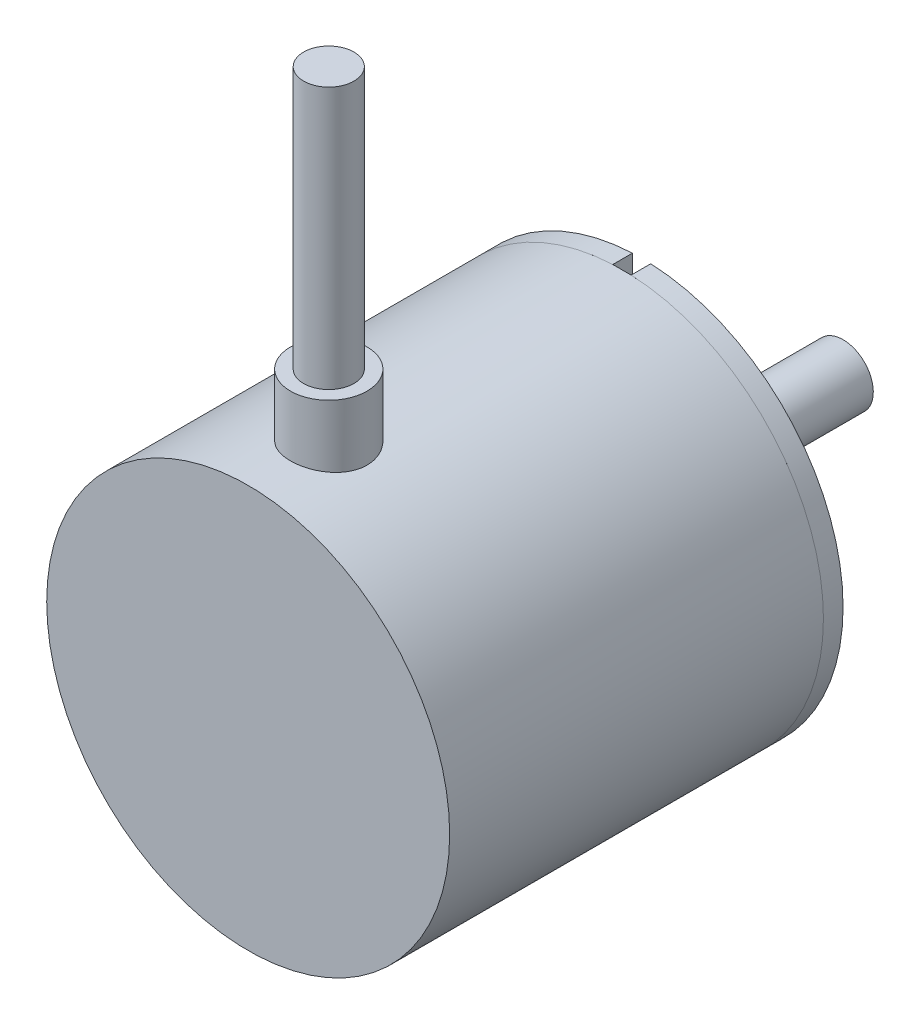
SolidWorks part; units mm, degrees
ref_plane "Front Plane" through (0, 0, 0) normal (0, 0, 1) x (1, 0, 0)
ref_plane "Top Plane" through (0, 0, 0) normal (0, 1, 0) x (1, 0, 0)
ref_plane "Right Plane" through (0, 0, 0) normal (1, 0, 0) x (0, 0, -1)
sketch "Sketch1" plane through (0, 0, 0) normal (0, 0, 1) x (1, 0, 0)
  circle A0 centre (0, 0) radius 20
extrude "Boss-Extrude1" add sketch "Sketch1" along normal blind 1.95
sketch "Sketch2" plane through (0, 0, 0) normal (0, 0, -1) x (-1, 0, 0)
  circle A0 centre (0, 0) radius 10
extrude "Boss-Extrude2" add sketch "Sketch2" along normal blind 5
sketch "Sketch3" plane through (0, 0, -5) normal (0, 0, -1) x (-1, 0, 0)
  circle A0 centre (0, 0) radius 3
extrude "Boss-Extrude3" add sketch "Sketch3" along normal blind 15
sketch "Sketch4" plane through (0, 0, 0) normal (0, 0, -1) x (-1, 0, 0)
  line L0 (0, 15) -> (-12.9904, -7.5) construction
  circle A0 centre (0, 0) radius 15 construction
  circle A1 centre (0, 15) radius 1
  circle A2 centre (12.9904, -7.5) radius 1
  circle A3 centre (-12.9904, -7.5) radius 1
  point P11 (0, 0.1678)
  point P12 (0, 0)
  dimension "D1" = 3
extrude "Cut-Extrude1" cut sketch "Sketch4" against normal blind 10
sketch "Sketch5" plane through (0, 0, 0) normal (0, 0, -1) x (-1, 0, 0)
  line L0 (0.91, 20) -> (-0.91, 20)
  line L1 (0, 20) -> (0, 18.0795)
  line L2 (-0.91, 20) -> (-0.91, 18.0795)
  line L3 (-0.91, 18.0795) -> (0.91, 18.0795)
  line L4 (0.91, 20) -> (0.91, 18.0795)
  circle A0 centre (0, 0) radius 20 construction
  circle M4 centre (0, 0) radius 20
extrude "Cut-Extrude2" cut sketch "Sketch5" against normal blind 2.3 contours L4 L1 L3 M4 | L2 L3 L1 M4
sketch "Sketch6" plane through (0, 0, 1.95) normal (0, 0, 1) x (1, 0, 0)
  circle A0 centre (0, 0) radius 20
extrude "Boss-Extrude5" add sketch "Sketch6" along normal blind 37.1 separate body
sketch "Sketch7" plane through (0, 0, -5) normal (0, 0, -1) x (-1, 0, 0)
  circle A1 centre (0, 0) radius 7.5
extrude "Cut-Extrude3" cut sketch "Sketch7" against normal blind 0.1
ref_plane "Plane1" through (0, 0, 31.05) normal (0, 0, 1) x (1, 0, 0)
sketch "Sketch8" plane through (0, 0, 31.05) normal (0, 0, 1) x (1, 0, 0)
  line L2 (0, 20) -> (0, -20) construction
  circle A0 centre (0, 0) radius 20 construction
sketch "Sketch9" plane through (0, 0, 0) normal (0, 1, 0) x (1, 0, 0)
  line L0 (-22, -31.05) -> (22, -31.05) construction
  circle A0 centre (0, -31.05) radius 3.8
extrude "Boss-Extrude6" add sketch "Sketch9" along normal blind 26
sketch "Sketch10" plane through (0, 26, 0) normal (0, 1, 0) x (1, 0, 0)
  circle A0 centre (0, -31.05) radius 2.5
extrude "Boss-Extrude7" add sketch "Sketch10" along normal blind 26
sketch "Sketch11" plane through (0, 0, -20) normal (0, 0, -1) x (-1, 0, 0)
  line L0 (0, 3) -> (0, -2) construction
  line L1 (-2.9274, -2) -> (3.2004, -2)
  line L2 (3.2004, -2) -> (3.2004, -3.3197)
  line L3 (3.2004, -3.3197) -> (-2.9274, -3.3197)
  line L4 (-2.9274, -3.3197) -> (-2.9274, -2)
  circle A0 centre (0, 0) radius 3 construction
extrude "Cut-Extrude4" cut sketch "Sketch11" against normal blind 9
